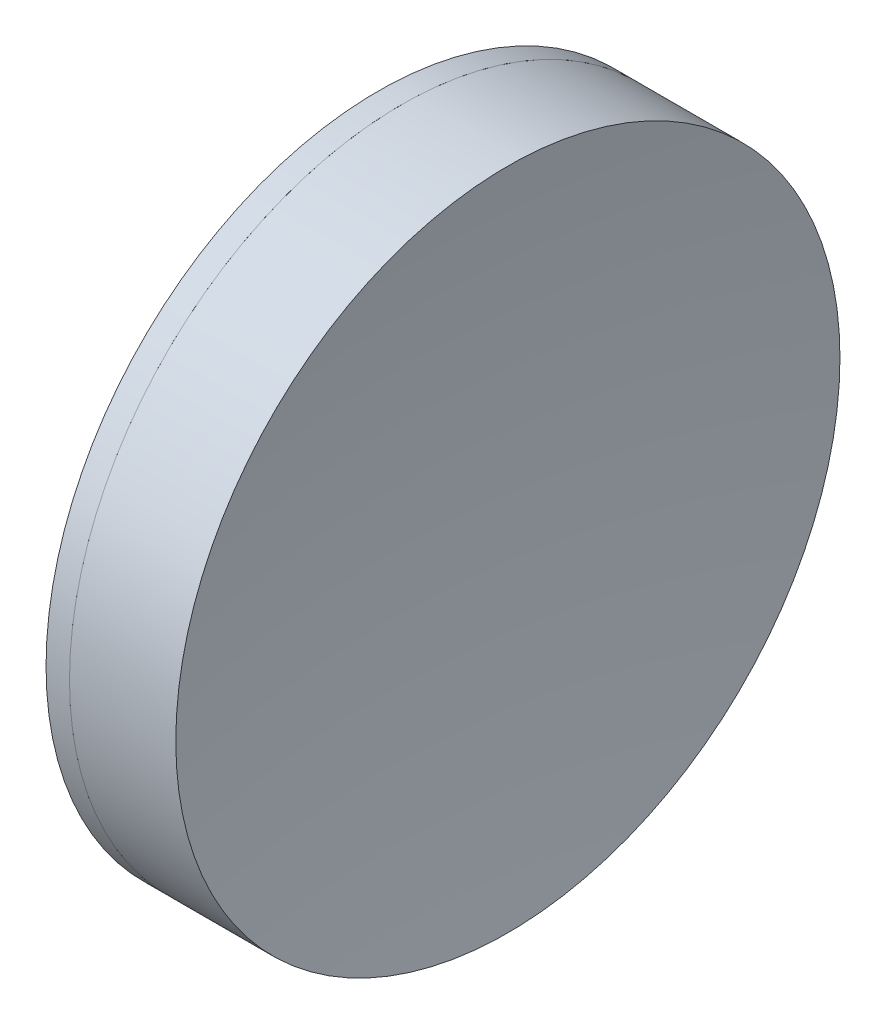
SolidWorks part; units mm, degrees
ref_plane "前视基准面" through (0, 0, 0) normal (0, 0, 1) x (1, 0, 0)
ref_plane "上视基准面" through (0, 0, 0) normal (0, 1, 0) x (1, 0, 0)
ref_plane "右视基准面" through (0, 0, 0) normal (1, 0, 0) x (0, 0, -1)
sketch "草图1" plane through (0, 0, 0) normal (0, 1, 0) x (1, 0, 0)
  line L0 (-0.8161, 0) -> (242.964, 0) construction
  line L1 (184.5397, -25.4) -> (186.3333, -25.4)
  line L2 (184.5397, 25.4) -> (186.3333, 25.4)
  arc A0 (186.3333, -25.4) -> (186.3333, 25.4) centre (86.3079, 0) ccw
  arc A1 (184.5397, 25.4) -> (184.5397, -25.4) centre (266.8079, 0) ccw
  point P10 (180.7079, 0)
  point P11 (189.5079, 0)
  dimension "D3" = 86.1
  dimension "D4" = 103.2
  dimension "D1" = 25.4
  dimension "D2" = 25.4
  dimension "D5" = 8.8
revolve "旋转1" add sketch "草图1" angle 360 about L0
sketch "草图2" plane through (0, 0, 0) normal (0, 1, 0) x (1, 0, 0)
  line L0 (-0.5519, 0) -> (242.9643, 0) construction
  line L2 (186.3333, 25.4) -> (194.4631, 25.4)
  line L3 (186.3333, -25.4) -> (194.4631, -25.4)
  arc A0 (194.4631, 25.4) -> (194.4631, -25.4) centre (358.4679, 0) ccw
  arc A1 (186.3333, -25.4) -> (186.3333, 25.4) centre (86.3079, 0) ccw construction
  arc A2 (186.3333, -25.4) -> (186.3333, 25.4) centre (86.3079, 0) ccw
  point P4 (189.5079, 0)
  point P8 (192.5079, 0)
  dimension "D1" = 165.96
  dimension "D2" = 3
revolve "旋转2" add sketch "草图2" angle 360 about L0
